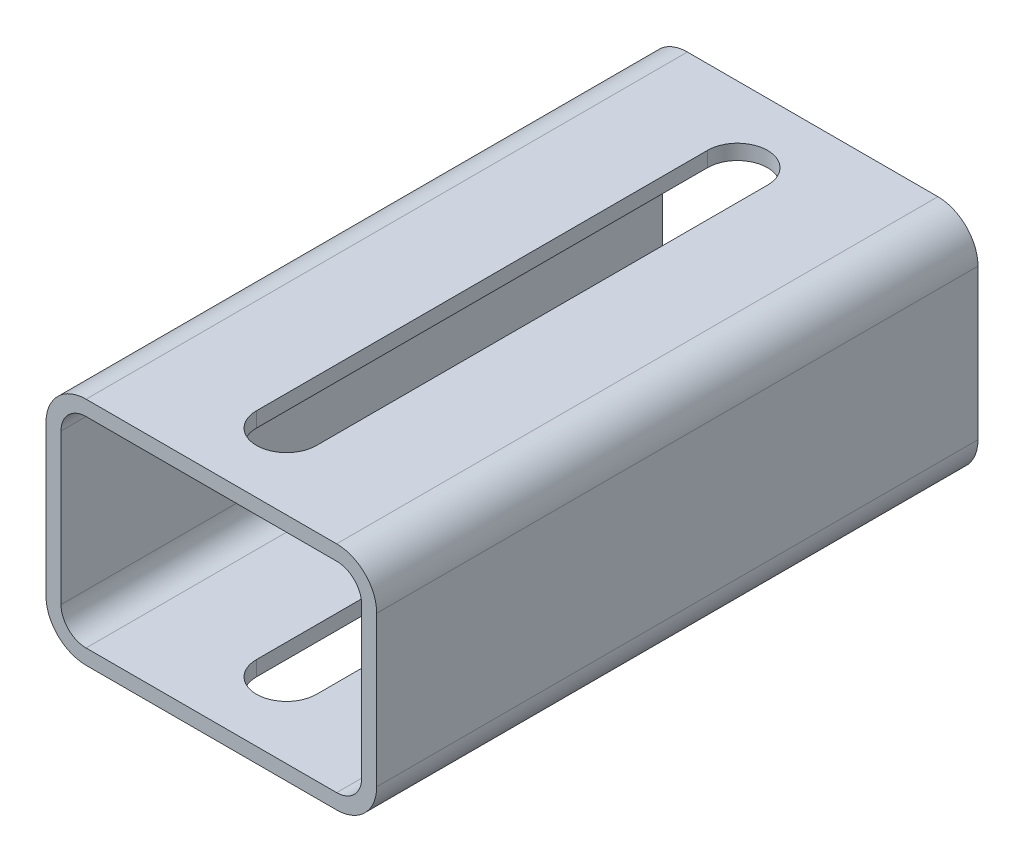
SolidWorks part; units mm, degrees
ref_plane "Front Plane" through (0, 0, 0) normal (0, 0, 1) x (1, 0, 0)
ref_plane "Top Plane" through (0, 0, 0) normal (0, 1, 0) x (1, 0, 0)
ref_plane "Right Plane" through (0, 0, 0) normal (1, 0, 0) x (0, 0, -1)
sketch "Sketch2" plane through (0, 0, 0) normal (0, 0, 1) x (1, 0, 0)
  line L1 (25, -20) -> (-25, -20)
  line L2 (30, -15) -> (30, 15)
  line L3 (25, 20) -> (-25, 20)
  line L4 (-30, -15) -> (-30, 15)
  line L5 (30, -20) -> (-30, 20) construction
  line L6 (30, 20) -> (-30, -20) construction
  arc A0 (-30, -15) -> (-25, -20) centre (-25, -15) ccw
  arc A1 (25, -20) -> (30, -15) centre (25, -15) ccw
  arc A2 (30, 15) -> (25, 20) centre (25, 15) ccw
  arc A3 (-30, 15) -> (-25, 20) centre (-25, 15) cw
  point P0 (0, 0)
  dimension "D3" = 5
  dimension "D1" = 60
  dimension "D2" = 40
extrude "Extrude-Thin1" add sketch "Sketch2" along normal mid plane 120 thin thin type one direction wall 3
sketch "Sketch3" plane through (0, 23, 0) normal (0, 1, 0) x (1, 0, 0)
  line L0 (0, -45) -> (0, 45) construction
  line L3 (-6, -45) -> (-6, 45)
  line L4 (6, -45) -> (6, 45)
  arc A2 (-6, -45) -> (6, -45) centre (0, -45) ccw
  arc A3 (6, 45) -> (-6, 45) centre (0, 45) ccw
  point P3 (0, 0)
  dimension "D1" = 6
  dimension "D2" = 90
  dimension "D3" = 45
extrude "Cut-Extrude1" cut sketch "Sketch3" against normal through all
